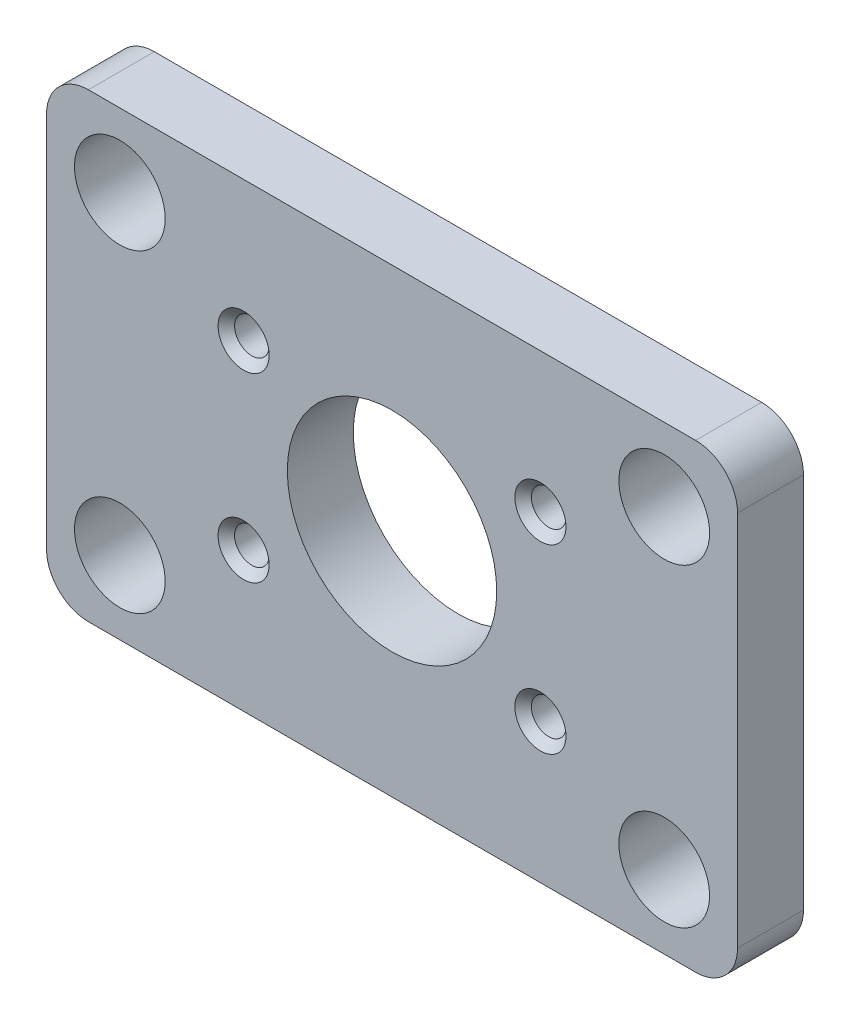
SolidWorks part; units mm, degrees
ref_plane "Front Plane" through (0, 0, 0) normal (0, 0, 1) x (1, 0, 0)
ref_plane "Top Plane" through (0, 0, 0) normal (0, 1, 0) x (1, 0, 0)
ref_plane "Right Plane" through (0, 0, 0) normal (1, 0, 0) x (0, 0, -1)
sketch "Sketch1" plane through (0, 0, 0) normal (0, 0, 1) x (1, 0, 0)
  line L0 (0, 0) -> (-20.955, 0) construction
  line L1 (20.955, -13.97) -> (-20.955, -13.97)
  line L2 (20.955, -13.97) -> (20.955, 13.97)
  line L3 (20.955, 13.97) -> (-20.955, 13.97)
  line L4 (-20.955, -13.97) -> (-20.955, 13.97)
  line L5 (20.955, -13.97) -> (-20.955, 13.97) construction
  line L6 (20.955, 13.97) -> (-20.955, -13.97) construction
  line L7 (0, 0) -> (0, 13.97) construction
  line L8 (-9.0005, 5.5004) -> (9.0005, 5.5004) construction
  line L9 (9.0005, 5.5004) -> (9.0005, -5.5004) construction
  circle A0 centre (-16.51, 9.525) radius 2.75
  circle A1 centre (16.51, 9.525) radius 2.75
  circle A2 centre (16.51, -9.525) radius 2.75
  circle A3 centre (-16.51, -9.525) radius 2.75
  circle A4 centre (-9.0005, 5.5004) radius 1.05
  circle A5 centre (9.0005, -5.5004) radius 1.05
  circle A6 centre (0, 0) radius 6.35
  circle A7 centre (-9.0005, -5.5004) radius 1.05
  circle A8 centre (9.0005, 5.5004) radius 1.05
  point P0 (0, 0)
  point P22 (0, 5.5004)
  point P24 (9.0005, 0)
  point P29 (-16.51, 9.525)
  point P30 (16.51, 9.525)
  point P31 (16.51, -9.525)
  point P32 (-16.51, -9.525)
  point P33 (0, 0)
  dimension "D3" = 5.5
  dimension "D6" = 2.1
  dimension "D9" = 12.7
  dimension "D1" = 27.94
  dimension "D2" = 41.91
  dimension "D4" = 19.05
  dimension "D5" = 33.02
  dimension "D7" = 18.001
  dimension "D8" = 11.0007
extrude "Boss-Extrude1" add sketch "Sketch1" along normal blind 4
fillet "Fillet1" radius 2.54 4 edges at (20.955, 13.97, 2) (20.955, -13.97, 2) (-20.955, -13.97, 2) (-20.955, 13.97, 2)
chamfer "Chamfer1" distance 0.5 angle 45 4 edges at (10.0505, -5.5004, 4) (7.9505, 5.5004, 4) (-10.0505, -5.5004, 4) (-7.9505, 5.5004, 4)
